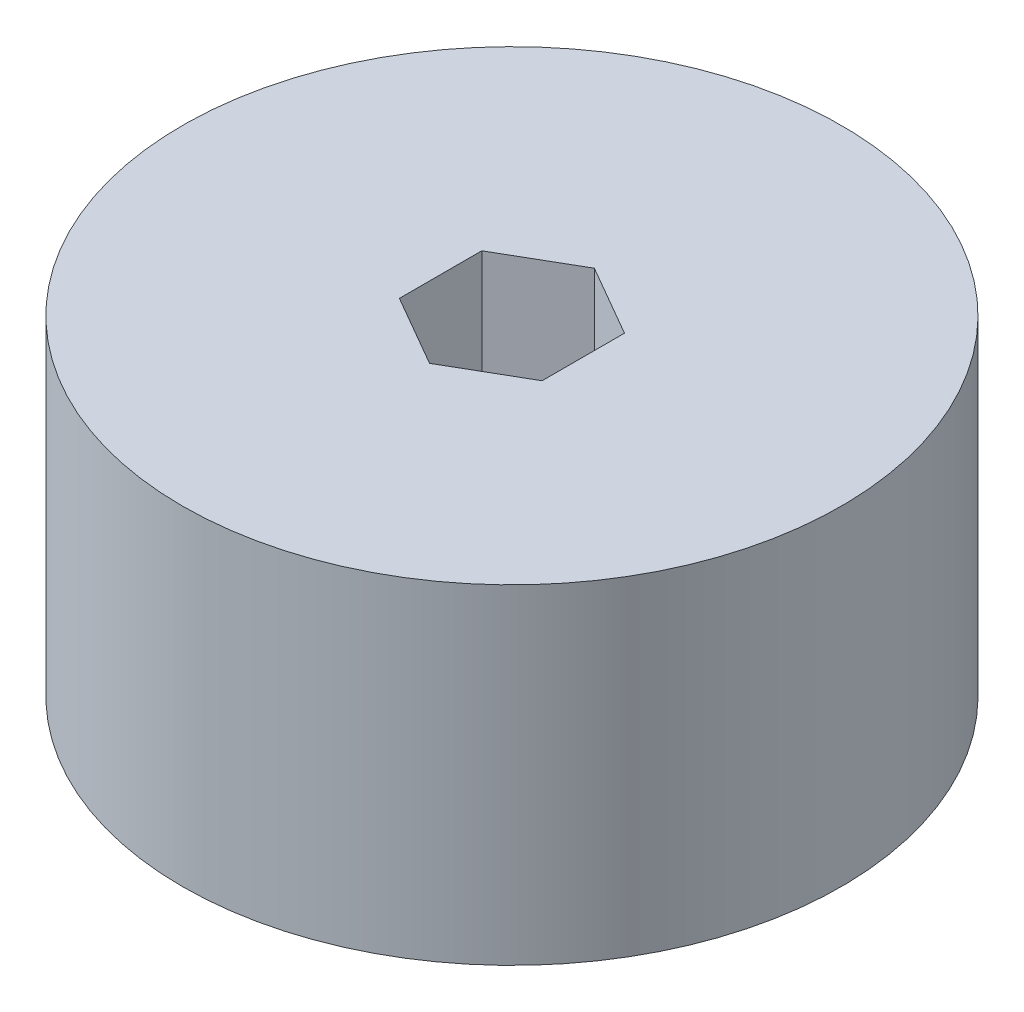
SolidWorks part; units mm, degrees
ref_plane "Front Plane" through (0, 0, 0) normal (0, 0, 1) x (1, 0, 0)
ref_plane "Top Plane" through (0, 0, 0) normal (0, 1, 0) x (1, 0, 0)
ref_plane "Right Plane" through (0, 0, 0) normal (1, 0, 0) x (0, 0, -1)
sketch "Sketch1" plane through (0, 0, 0) normal (0, 1, 0) x (1, 0, 0)
  line L1 (5.4993, -3.175) -> (5.4993, 3.175)
  line L2 (5.4993, 3.175) -> (0, 6.35)
  line L3 (0, 6.35) -> (-5.4993, 3.175)
  line L4 (-5.4993, 3.175) -> (-5.4993, -3.175)
  line L5 (-5.4993, -3.175) -> (0, -6.35)
  line L6 (0, -6.35) -> (5.4993, -3.175)
  circle A0 centre (0, 0) radius 25.4
  circle A1 centre (0, 0) radius 6.35 construction
  dimension "D1" = 50.8
  dimension "D2" = 12.7
extrude "Boss-Extrude1" add sketch "Sketch1" along normal blind 25.4
